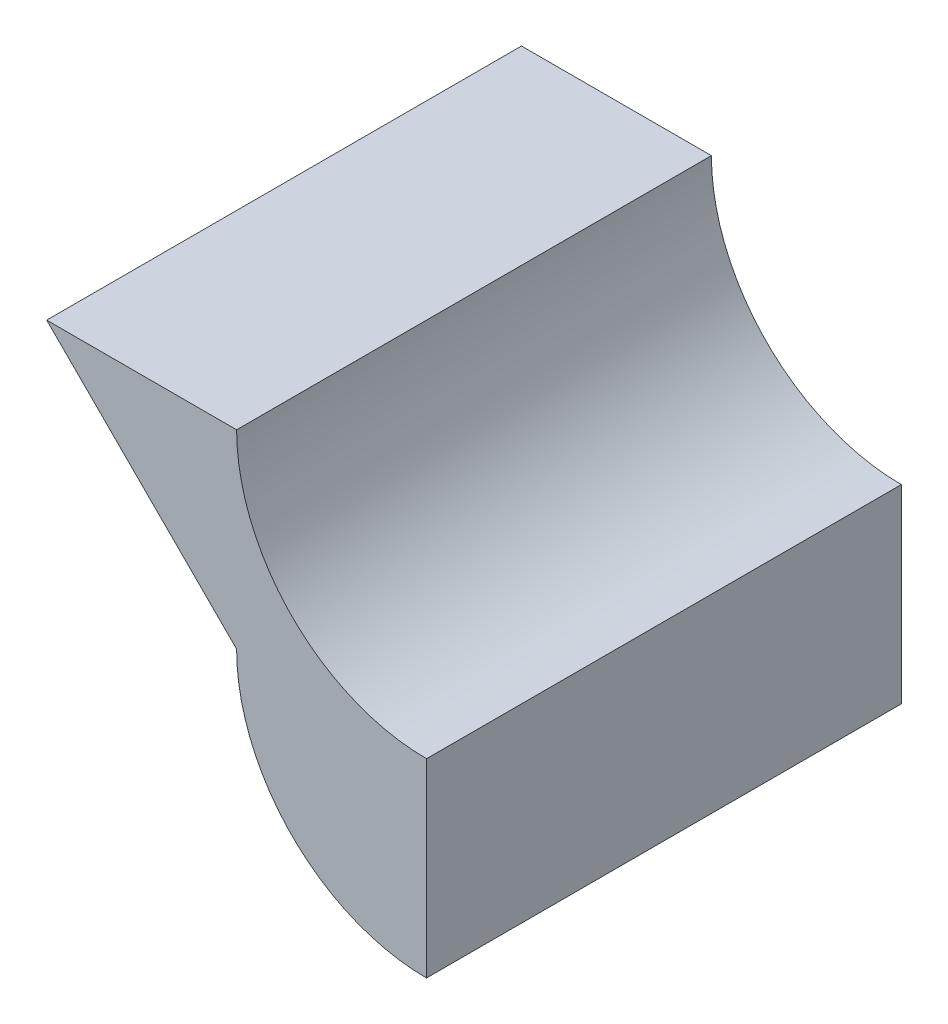
SolidWorks part; units mm, degrees
ref_plane "Front Plane" through (0, 0, 0) normal (0, 0, 1) x (1, 0, 0)
ref_plane "Top Plane" through (0, 0, 0) normal (0, 1, 0) x (1, 0, 0)
ref_plane "Right Plane" through (0, 0, 0) normal (1, 0, 0) x (0, 0, -1)
sketch "Sketch1" plane through (0, 0, 0) normal (0, 0, 1) x (1, 0, 0)
  line L0 (-20, 20) -> (-10, 20)
  line L1 (0, 10) -> (0, 0)
  line L2 (-20, 20) -> (-10, 10)
  arc A0 (-10, 10) -> (0, 0) centre (0, 10) ccw
  arc A1 (-10, 20) -> (0, 10) centre (0, 20) ccw
  dimension "D3" = 10
  dimension "D1" = 10
  dimension "D2" = 10
extrude "Boss-Extrude1" add sketch "Sketch1" along normal blind 25
